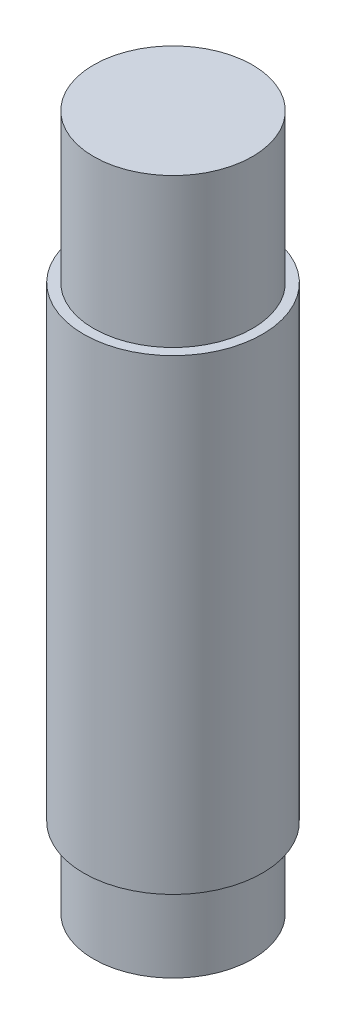
SolidWorks part; units mm, degrees
ref_plane "Front Plane" through (0, 0, 0) normal (0, 0, 1) x (1, 0, 0)
ref_plane "Top Plane" through (0, 0, 0) normal (0, 1, 0) x (1, 0, 0)
ref_plane "Right Plane" through (0, 0, 0) normal (1, 0, 0) x (0, 0, -1)
sketch "Sketch1" plane through (0, 0, 0) normal (0, 1, 0) x (1, 0, 0)
  circle A0 centre (0, 0) radius 8
  dimension "D1" = 16
extrude "Boss-Extrude1" add sketch "Sketch1" along normal blind 8
sketch "Sketch2" plane through (0, 8, 0) normal (0, 1, 0) x (1, 0, 0)
  circle A0 centre (0, 0) radius 9
  dimension "D1" = 18
extrude "Boss-Extrude2" add sketch "Sketch2" along normal blind 47
sketch "Sketch3" plane through (0, 55, 0) normal (0, 1, 0) x (1, 0, 0)
  circle A0 centre (0, 0) radius 8
  dimension "D1" = 16
extrude "Boss-Extrude3" add sketch "Sketch3" along normal blind 15
